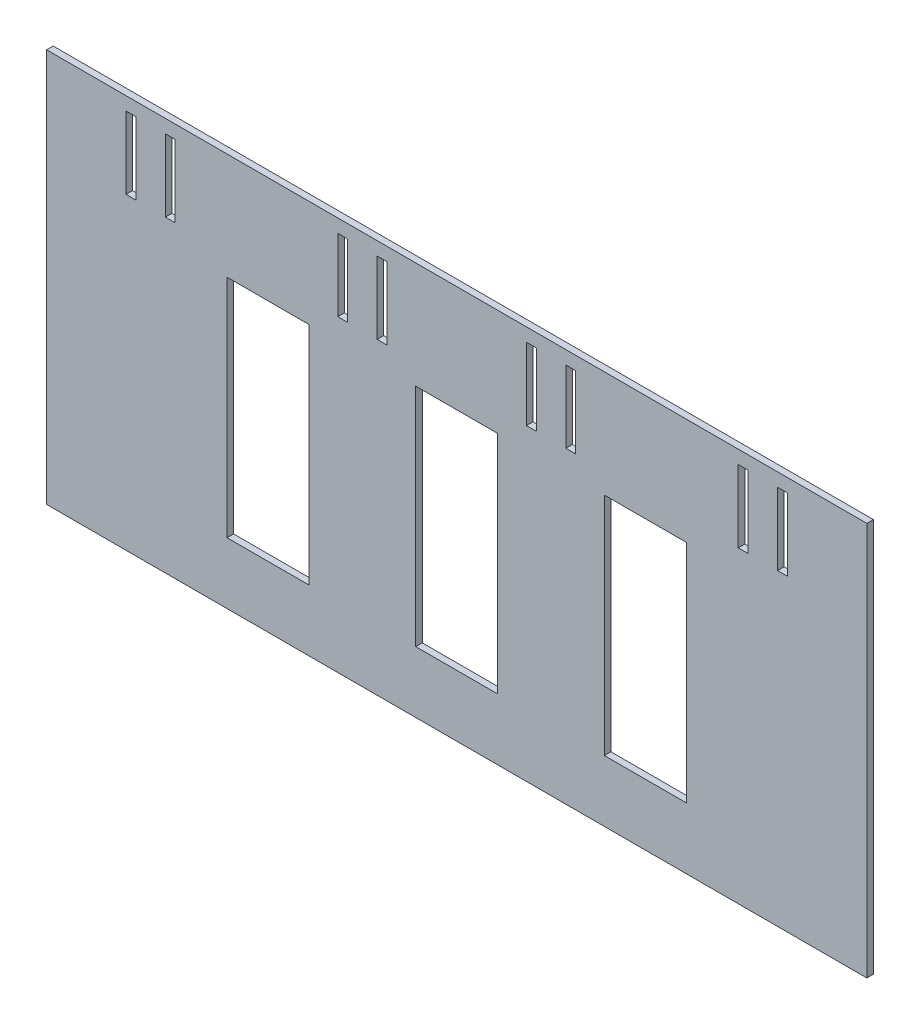
SolidWorks part; units mm, degrees
material "AISI 304"
ref_plane "前视基准面" through (0, 0, 0) normal (0, 0, 1) x (1, 0, 0)
ref_plane "上视基准面" through (0, 0, 0) normal (0, 1, 0) x (1, 0, 0)
ref_plane "右视基准面" through (0, 0, 0) normal (1, 0, 0) x (0, 0, -1)
sketch "草图1" plane through (0, 0, 0) normal (0, 0, 1) x (1, 0, 0)
  line L1 (-39.4185, 132.6579) -> (210.5815, 132.6579)
  line L2 (-39.4185, 132.6579) -> (-39.4185, 12.6579)
  line L3 (-39.4185, 12.6579) -> (210.5815, 12.6579)
  line L4 (210.5815, 132.6579) -> (210.5815, 12.6579)
extrude "凸台-拉伸1" add sketch "草图1" along normal blind 2
sketch "草图2" plane through (0, 0, 2) normal (0, 0, 1) x (1, 0, 0)
  line L0 (-39.4185, 132.6579) -> (-39.4185, 12.6579) construction
  line L1 (-15.2185, 128.5929) -> (-12.2185, 128.5929)
  line L2 (-15.2185, 128.5929) -> (-15.2185, 106.5929)
  line L3 (-15.2185, 106.5929) -> (-12.2185, 106.5929)
  line L4 (-12.2185, 128.5929) -> (-12.2185, 106.5929)
  line L5 (-3.2185, 128.5929) -> (-0.2185, 128.5929)
  line L6 (-3.2185, 128.5929) -> (-3.2185, 106.5929)
  line L7 (-3.2185, 106.5929) -> (-0.2185, 106.5929)
  line L8 (-0.2185, 128.5929) -> (-0.2185, 106.5929)
  line L9 (49.3315, 128.5929) -> (52.3315, 128.5929)
  line L10 (49.3315, 128.5929) -> (49.3315, 106.5929)
  line L11 (49.3315, 106.5929) -> (52.3315, 106.5929)
  line L12 (52.3315, 128.5929) -> (52.3315, 106.5929)
  line L13 (61.3315, 128.5929) -> (64.3315, 128.5929)
  line L14 (61.3315, 128.5929) -> (61.3315, 106.5929)
  line L15 (61.3315, 106.5929) -> (64.3315, 106.5929)
  line L16 (64.3315, 128.5929) -> (64.3315, 106.5929)
  line L17 (106.8315, 128.5929) -> (109.8315, 128.5929)
  line L18 (106.8315, 128.5929) -> (106.8315, 106.5929)
  line L19 (106.8315, 106.5929) -> (109.8315, 106.5929)
  line L20 (109.8315, 128.5929) -> (109.8315, 106.5929)
  line L21 (118.8315, 128.5929) -> (121.8315, 128.5929)
  line L22 (118.8315, 128.5929) -> (118.8315, 106.5929)
  line L23 (118.8315, 106.5929) -> (121.8315, 106.5929)
  line L24 (121.8315, 128.5929) -> (121.8315, 106.5929)
  line L25 (171.3815, 128.5929) -> (174.3815, 128.5929)
  line L26 (171.3815, 128.5929) -> (171.3815, 106.5929)
  line L27 (171.3815, 106.5929) -> (174.3815, 106.5929)
  line L28 (174.3815, 128.5929) -> (174.3815, 106.5929)
  line L29 (183.3815, 128.5929) -> (186.3815, 128.5929)
  line L30 (183.3815, 128.5929) -> (183.3815, 106.5929)
  line L31 (183.3815, 106.5929) -> (186.3815, 106.5929)
  line L32 (186.3815, 128.5929) -> (186.3815, 106.5929)
  line L33 (210.5815, 12.6579) -> (210.5815, 132.6579) construction
  point P34 (-13.7185, 128.5929)
  point P35 (-1.7185, 128.5929)
  point P36 (50.8315, 128.5929)
  point P37 (62.8315, 128.5929)
  point P38 (108.3315, 128.5929)
  point P39 (120.3315, 128.5929)
  point P40 (172.8815, 128.5929)
  point P41 (184.8815, 128.5929)
  dimension "D1" = 24.2
  dimension "D2" = 12
  dimension "D3" = 12
  dimension "D4" = 12
  dimension "D5" = 12
  dimension "D6" = 90.25
  dimension "D7" = 25.7
  dimension "D8" = 90.25
extrude "切除-拉伸1" cut sketch "草图2" against normal blind 2
sketch "草图4" plane through (0, 0, 0) normal (0, 0, -1) x (-1, 0, 0)
  line L0 (-130.5815, 117.005) -> (-130.5815, 58.5885) construction
  line L1 (-155.5815, 31.3702) -> (-130.5815, 31.3702)
  line L2 (-155.5815, 31.3702) -> (-155.5815, 100.1276)
  line L3 (-155.5815, 100.1276) -> (-130.5815, 100.1276)
  line L4 (-130.5815, 31.3702) -> (-130.5815, 100.1276)
  line L5 (-73.0815, 117.005) -> (-73.0815, 58.5885) construction
  line L6 (-98.0815, 31.3702) -> (-73.0815, 31.3702)
  line L7 (-98.0815, 31.3702) -> (-98.0815, 100.1276)
  line L8 (-98.0815, 100.1276) -> (-73.0815, 100.1276)
  line L9 (-73.0815, 31.3702) -> (-73.0815, 100.1276)
  line L10 (-15.5815, 117.005) -> (-15.5815, 58.5885) construction
  line L11 (-40.5815, 31.3702) -> (-15.5815, 31.3702)
  line L12 (-40.5815, 31.3702) -> (-40.5815, 100.1276)
  line L13 (-40.5815, 100.1276) -> (-15.5815, 100.1276)
  line L14 (-15.5815, 31.3702) -> (-15.5815, 100.1276)
extrude "切除-拉伸3" cut sketch "草图4" against normal blind 10
